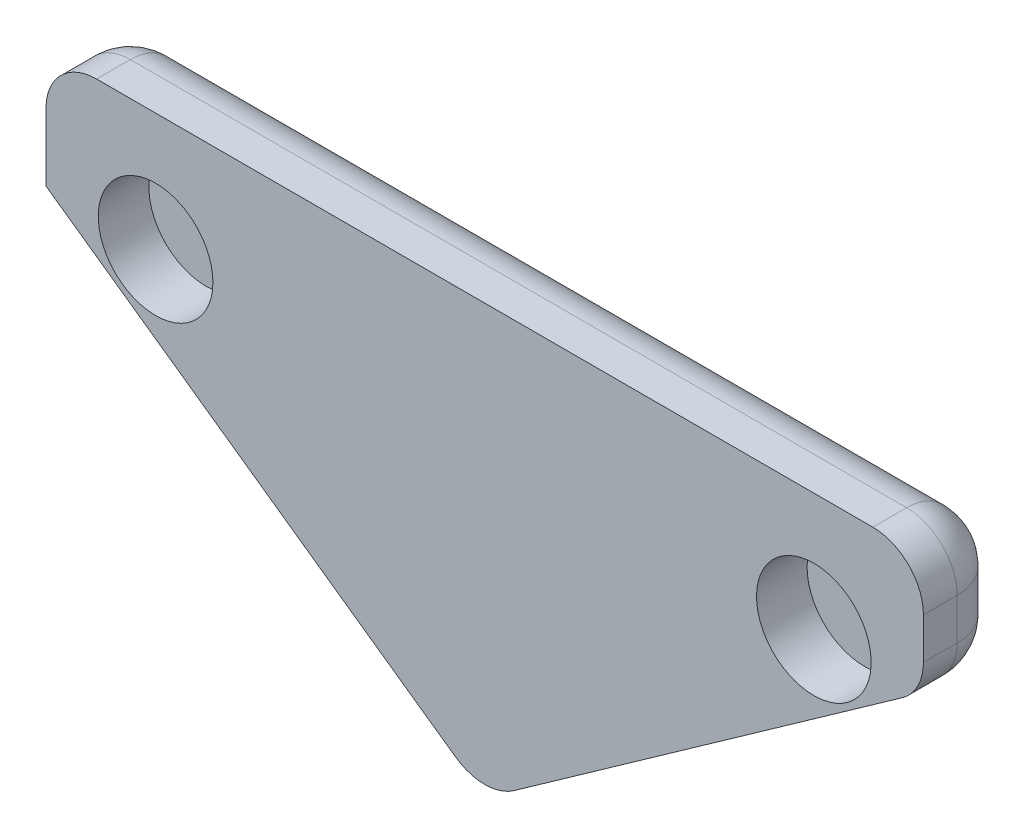
SolidWorks part; units mm, degrees
ref_plane "Front Plane" through (0, 0, 0) normal (0, 0, 1) x (1, 0, 0)
ref_plane "Top Plane" through (0, 0, 0) normal (0, 1, 0) x (1, 0, 0)
ref_plane "Right Plane" through (0, 0, 0) normal (1, 0, 0) x (0, 0, -1)
sketch "Sketch1" plane through (0, 0, 0) normal (0, 0, 1) x (1, 0, 0)
  line L0 (-7.5642, 12.7) -> (-7.5642, 9.2)
  line L3 (-7.5642, 9.2) -> (5.4458, 0)
  line L4 (5.4458, 0) -> (5.4458, 12.7)
  line L6 (5.4458, 12.7) -> (-7.5642, 12.7)
  line L7 (-4.3142, 12.7) -> (-4.3142, 5.95) construction
  line L8 (-7.5642, 9.2) -> (5.4458, 9.2) construction
  dimension "D1" = 3.5
  dimension "D2" = 3.25
  dimension "D3" = 12.7
  dimension "D5" = 13.01
extrude "Boss-Extrude1" add sketch "Sketch1" along normal blind 2.5
sketch "Sketch2" plane through (0, 0, 2.5) normal (0, 0, 1) x (1, 0, 0)
  line L0 (-7.5642, 9.2) -> (5.4458, 9.2) construction
  line L1 (-7.5642, 12.7) -> (-7.5642, 9.2) construction
  line L2 (5.4458, 0) -> (5.4458, 12.7) construction
  line L3 (-4.3142, 12.7) -> (-4.3142, 0) construction
  line L4 (5.4458, 12.7) -> (-7.5642, 12.7) construction
  circle A0 centre (-4.3142, 9.2) radius 1.7
  dimension "D1" = 3.5
  dimension "D2" = 3.25
extrude "Cut-Extrude1" cut sketch "Sketch2" against normal blind 1.5
mirror "Mirror2" about plane through (5.4458, 0, 2.5) normal (-1, 0, 0) of bodies 103
fillet "Fillet1" radius 1.5 9 edges at (-7.5642, 12.7, 1.25) (-7.5642, 10.95, 0) (5.4458, 12.7, 0) (18.4558, 12.7, 1.25) (18.4558, 9.2, 1.25) (18.4558, 10.95, 0) (11.9508, 4.6, 0) (5.4458, 0, 1.25) (-1.0592, 4.6, 0)
